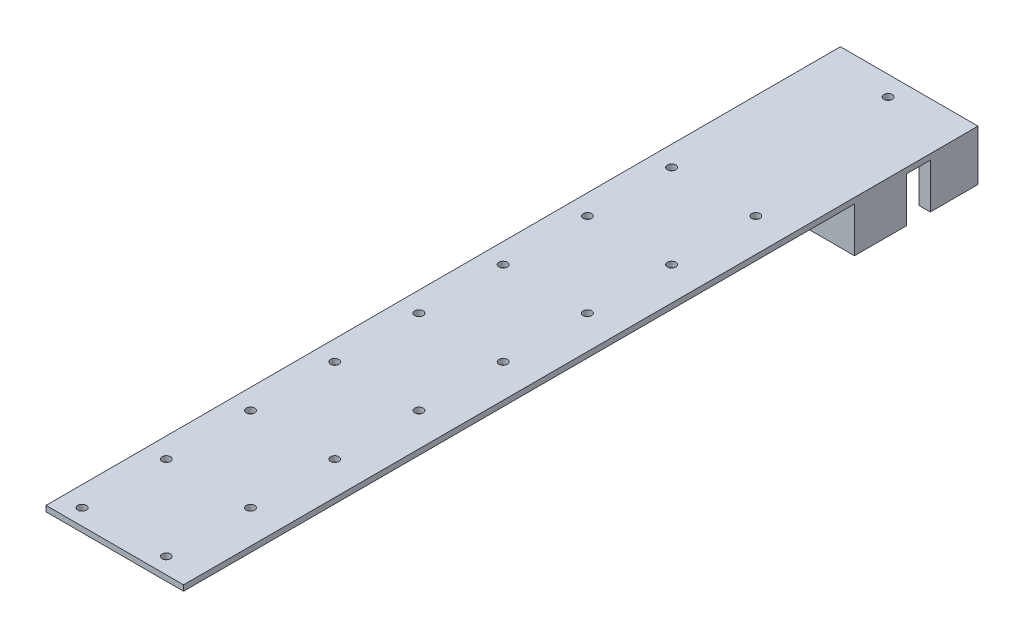
SolidWorks part; units mm, degrees
material "Cuivre"
ref_plane "Plan de face" through (0, 0, 0) normal (0, 0, 1) x (1, 0, 0)
ref_plane "Plan de dessus" through (0, 0, 0) normal (0, 1, 0) x (1, 0, 0)
ref_plane "Plan de droite" through (0, 0, 0) normal (1, 0, 0) x (0, 0, -1)
sketch "Esquisse1" plane through (0, 0, 0) normal (0, 1, 0) x (1, 0, 0)
  line L0 (12.65, 74.2) -> (-17.35, 74.2) construction
  line L1 (-24.5, -141.5) -> (24.5, -141.5)
  line L2 (-24.5, -141.5) -> (-24.5, 141.5)
  line L3 (-24.5, 141.5) -> (24.5, 141.5)
  line L4 (24.5, -141.5) -> (24.5, 141.5)
  line L5 (-24.5, -141.5) -> (24.5, 141.5) construction
  line L6 (-24.5, 141.5) -> (24.5, -141.5) construction
  line L7 (12.65, 74.2) -> (12.65, 44.2) construction
  circle A0 centre (12.65, 74.2) radius 1.5
  circle A1 centre (-17.35, 74.2) radius 1.5
  circle A2 centre (-17.35, 44.2) radius 1.5
  circle A3 centre (-17.35, 14.2) radius 1.5
  circle A4 centre (-17.35, -15.8) radius 1.5
  circle A5 centre (-17.35, -45.8) radius 1.5
  circle A6 centre (-17.35, -75.8) radius 1.5
  circle A7 centre (-17.35, -105.8) radius 1.5
  circle A8 centre (-17.35, -135.8) radius 1.5
  circle A9 centre (12.65, 44.2) radius 1.5
  circle A10 centre (12.65, 14.2) radius 1.5
  circle A11 centre (12.65, -15.8) radius 1.5
  circle A12 centre (12.65, -45.8) radius 1.5
  circle A13 centre (12.65, -75.8) radius 1.5
  circle A14 centre (12.65, -105.8) radius 1.5
  circle A15 centre (12.65, -135.8) radius 1.5
  point P0 (0, 0)
  dimension "D5" = 3
  dimension "D1" = 49
  dimension "D2" = 283
  dimension "D3" = 67.3
  dimension "D4" = 11.85
  dimension "D8" = 90
  dimension "D9" = 30
  dimension "D10" = 30
  dimension "D6" = 2
  dimension "D7" = 8
extrude "Boss.-Extru.1" add sketch "Esquisse1" along normal blind 2
sketch "Esquisse2" plane through (0, 0, 0) normal (0, -1, 0) x (1, 0, 0)
  line L0 (24.5, 141.5) -> (24.5, -141.5) construction
  line L1 (-18.3, -97.5) -> (24.5, -97.5)
  line L2 (-18.3, -97.5) -> (-18.3, -116.1)
  line L3 (-18.3, -116.1) -> (24.5, -116.1)
  line L4 (24.5, -97.5) -> (24.5, -116.1)
  line L5 (-23.1, -124.5) -> (-19.1, -124.5)
  line L6 (-23.1, -124.5) -> (-23.1, -141.5)
  line L7 (-23.1, -141.5) -> (-19.1, -141.5)
  line L8 (-19.1, -124.5) -> (-19.1, -141.5)
  line L9 (20.5, -124.5) -> (24.5, -124.5)
  line L10 (20.5, -124.5) -> (20.5, -141.5)
  line L11 (20.5, -141.5) -> (24.5, -141.5)
  line L12 (24.5, -124.5) -> (24.5, -141.5)
  line L13 (24.5, -141.5) -> (-24.5, -141.5) construction
  line L14 (-24.5, -141.5) -> (-24.5, 141.5) construction
  point P16 (0, 0)
  dimension "D1" = 18.6
  dimension "D2" = 42.8
  dimension "D3" = 25.4
  dimension "D4" = 4
  dimension "D5" = 17
  dimension "D6" = 4
  dimension "D7" = 17
  dimension "D8" = 1.4
extrude "Boss.-Extru.2" add sketch "Esquisse2" along normal blind 16
sketch "Esquisse3" plane through (0, 0, 0) normal (0, -1, 0) x (1, 0, 0)
  line L0 (24.5, -116.1) -> (24.5, -124.5) construction
  line L1 (20.5, -141.5) -> (-19.1, -141.5) construction
  circle A0 centre (-0.5, -134.5) radius 1.5
  dimension "D1" = 3
  dimension "D2" = 25
  dimension "D3" = 7
extrude "Enlèv. mat.-Extru.1" cut sketch "Esquisse3" against normal blind 16
